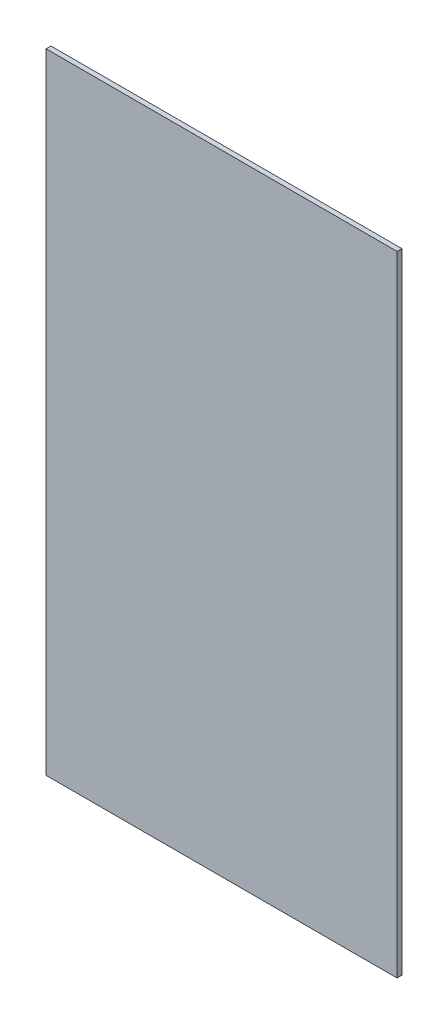
SolidWorks part; units mm, degrees
material "ABS PC"
ref_plane "Front Plane" through (0, 0, 0) normal (0, 0, 1) x (1, 0, 0)
ref_plane "Top Plane" through (0, 0, 0) normal (0, 1, 0) x (1, 0, 0)
ref_plane "Right Plane" through (0, 0, 0) normal (1, 0, 0) x (0, 0, -1)
sketch "Sketch1" plane through (0, 0, 0) normal (0, 0, 1) x (1, 0, 0)
  line L0 (-10.0659, 50.1337) -> (-19.2734, 50.1337) construction
  line L1 (-19.2734, 50.1337) -> (-19.2734, 33.6237) construction
  line L8 (-19.2734, 33.6237) -> (-10.0659, 33.6237)
  line L9 (-10.0659, 33.6237) -> (-10.0659, 50.1337)
  line L10 (-10.0659, 50.1337) -> (-19.2734, 50.1337)
  line L11 (-19.2734, 50.1337) -> (-19.2734, 33.6237)
extrude "Boss-Extrude1" add sketch "Sketch1" along normal blind 0.127
